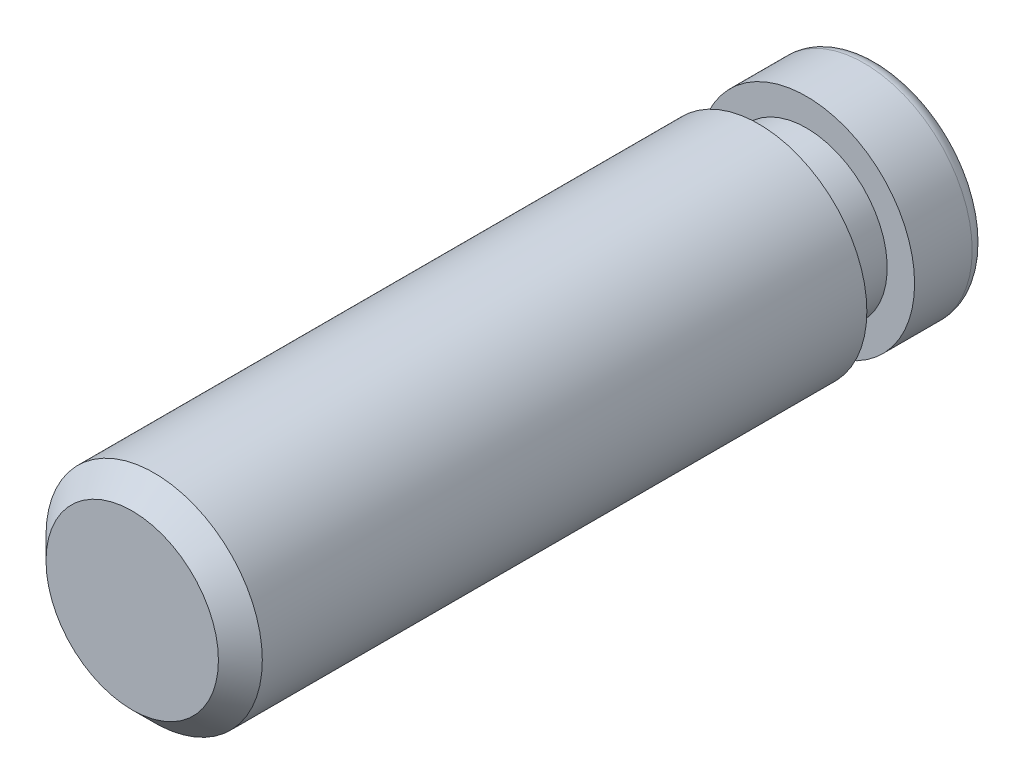
SolidWorks part; units mm, degrees
material "SS 304 (Default)"
ref_plane "Front Plane" through (0, 0, 0) normal (0, 0, 1) x (1, 0, 0)
ref_plane "Top Plane" through (0, 0, 0) normal (0, 1, 0) x (1, 0, 0)
ref_plane "Right Plane" through (0, 0, 0) normal (1, 0, 0) x (0, 0, -1)
sketch "Sketch1" plane through (0, 0, 0) normal (0, 0, 1) x (1, 0, 0)
  circle A0 centre (0, 0) radius 1.9558
  dimension "D1" = 3.9116
extrude "Extrude1" add sketch "Sketch1" along normal mid plane 13.4874
sketch "Sketch2" plane through (0, 0, 0) normal (0, 1, 0) x (1, 0, 0)
  line L0 (0, 10.0425) -> (0, -1.1158) construction
  line L1 (1.9558, -6.7437) -> (1.9558, 6.7437) construction
  line L2 (1.4605, 5.4483) -> (1.9558, 5.4483)
  line L3 (1.4605, 5.4483) -> (1.4605, 4.5847)
  line L4 (1.4605, 4.5847) -> (1.9558, 4.5847)
  line L5 (1.9558, 5.4483) -> (1.9558, 4.5847)
  line L6 (-1.9558, -6.7437) -> (1.9558, -6.7437) construction
  dimension "D1" = 1.4605
  dimension "D2" = 11.3284
  dimension "D3" = 0.8636
revolve "Cut-Revolve1" cut sketch "Sketch2" angle 360 about L0
fillet "Fillet1" radius 0.254 1 edges at (1.9558, 0, -6.7437)
chamfer "Chamfer1" distance 0.3969 angle 45 1 edges at (1.9558, 0, 6.7437)
